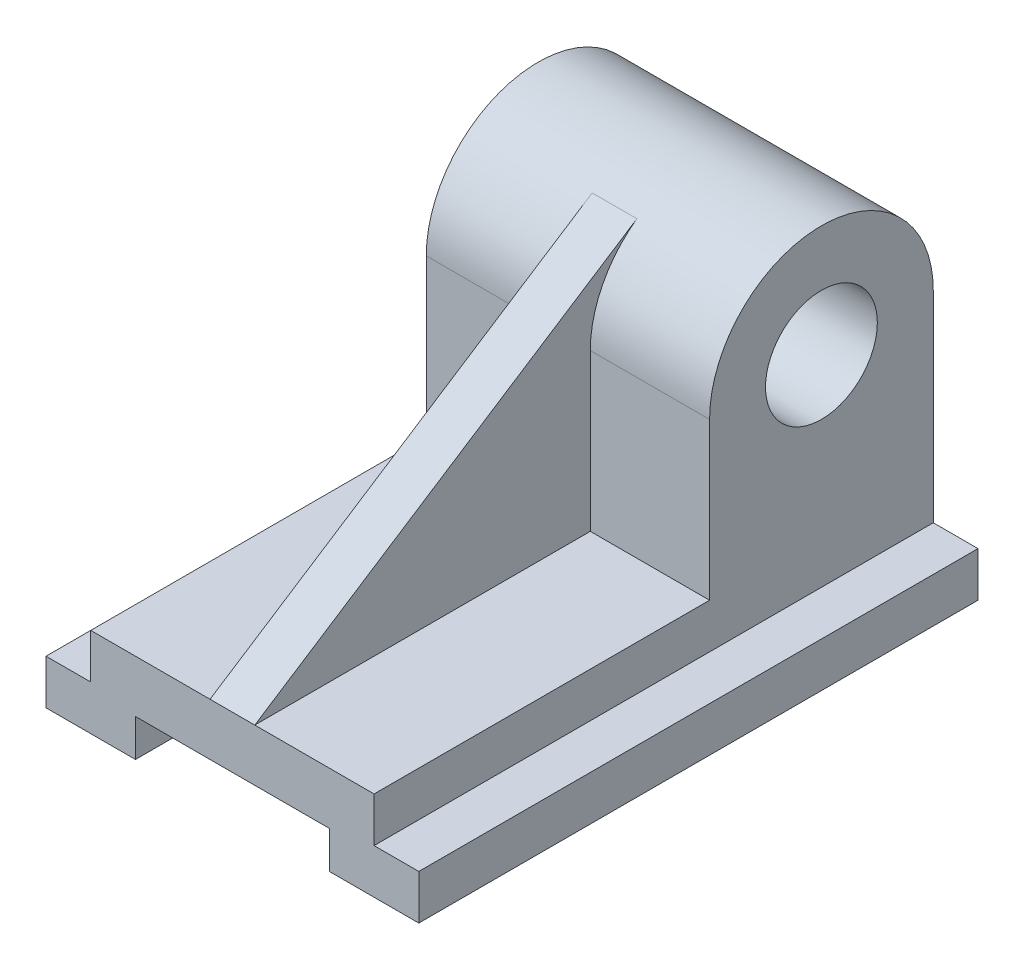
SolidWorks part; units mm, degrees
ref_plane "Front Plane" through (0, 0, 0) normal (0, 0, 1) x (1, 0, 0)
ref_plane "Top Plane" through (0, 0, 0) normal (0, 1, 0) x (1, 0, 0)
ref_plane "Right Plane" through (0, 0, 0) normal (1, 0, 0) x (0, 0, -1)
sketch "Sketch1" plane through (0, 0, 0) normal (0, 0, 1) x (1, 0, 0)
  line L0 (-50, 0) -> (-38, 0)
  line L1 (-50, -12) -> (-26, -12)
  line L2 (-50, -12) -> (-50, 0)
  line L3 (-38, 12) -> (38, 12)
  line L4 (50, -12) -> (50, 0)
  line L7 (-38, 0) -> (-38, 12)
  line L8 (-26, -12) -> (-26, -2)
  line L9 (-26, -2) -> (26, -2)
  line L10 (26, -2) -> (26, -12)
  line L11 (38, 12) -> (38, 0)
  line L12 (38, 0) -> (50, 0)
  line L13 (26, -12) -> (50, -12)
  point P0 (0, 0)
  dimension "D1" = 2
  dimension "D2" = 100
  dimension "D3" = 12
  dimension "D4" = 10
  dimension "D5" = 26
  dimension "D6" = 52
  dimension "D7" = 12
  dimension "D8" = 12
  dimension "D9" = 12
  dimension "D10" = 24
extrude "Boss-Extrude1" add sketch "Sketch1" along normal blind 150
sketch "Sketch4" plane through (0, 0, 0) normal (1, 0, 0) x (0, 0, -1)
  line L0 (0, 12) -> (0, 54)
  line L1 (-60, 12) -> (0, 12)
  line L2 (-60, 54) -> (-60, 12)
  line L3 (-150, 12) -> (0, 12) construction
  arc A0 (0, 54) -> (-60, 54) centre (-30, 54) ccw
  circle A2 centre (-30, 54) radius 15
  dimension "D3" = 60
  dimension "D4" = 30
  dimension "D5" = 30
  dimension "D1" = 42
  dimension "D2" = 60
extrude "Boss-Extrude2" add sketch "Sketch4" against normal mid plane 76
sketch "Sketch5" plane through (0, 0, 0) normal (1, 0, 0) x (0, 0, -1)
  line L0 (-150, 12) -> (-47.4968, 78.3692)
  arc A0 (0, 54) -> (-60, 54) centre (-30, 54) ccw construction
rib "Rib1" sketch "Sketch5" sketch "Sketch5" thickness 12 extrusion direction parallel to sketch draft on no parameters "D1"=12
